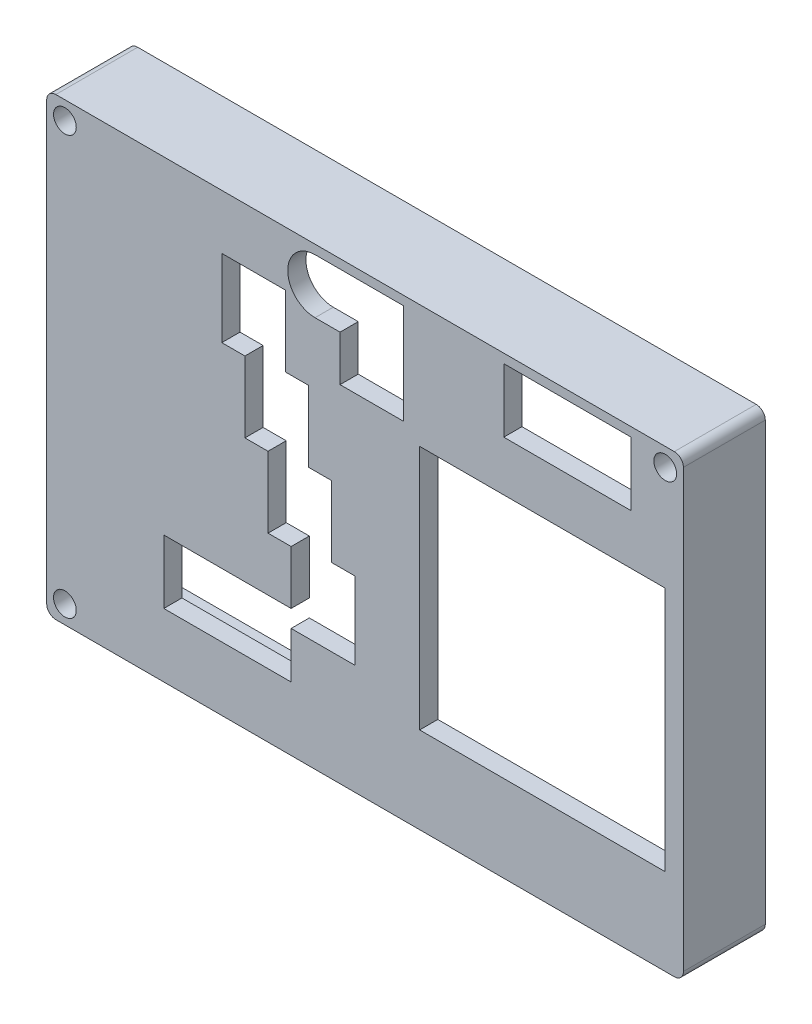
SolidWorks part; units mm, degrees
ref_plane "Front Plane" through (0, 0, 0) normal (0, 0, 1) x (1, 0, 0)
ref_plane "Top Plane" through (0, 0, 0) normal (0, 1, 0) x (1, 0, 0)
ref_plane "Right Plane" through (0, 0, 0) normal (1, 0, 0) x (0, 0, -1)
sketch "Sketch2" plane through (0, 0, 0) normal (0, 0, 1) x (1, 0, 0)
  line L0 (0, -55) -> (0, 55) construction
  line L1 (-35, 25) -> (35, 25)
  line L2 (-35, 25) -> (-35, -25)
  line L3 (-35, -25) -> (35, -25)
  line L4 (35, 25) -> (35, -25)
  line L5 (-35, 25) -> (35, -25) construction
  line L6 (-35, -25) -> (35, 25) construction
  line L7 (6, 11.5) -> (33, 11.5)
  line L8 (6, 11.5) -> (6, -15.5)
  line L9 (6, -15.5) -> (33, -15.5)
  line L10 (33, 11.5) -> (33, -15.5)
  line L11 (55, 0) -> (-55, 0) construction
  line L13 (-22.13, -11) -> (-8.13, -11)
  line L14 (-22.13, -11) -> (-22.13, -18)
  line L15 (-22.13, -18) -> (-8.13, -18)
  line L16 (-8.13, -12.9) -> (-8.13, -18)
  line L17 (-2.75, 24) -> (4.25, 24)
  line L19 (-2.75, 13) -> (4.25, 13)
  line L20 (4.25, 24) -> (4.25, 13)
  line L21 (-15.75, 19) -> (-8.75, 19)
  line L22 (-15.75, 19) -> (-15.75, 10.5)
  line L23 (-15.75, 10.5) -> (-13.21, 10.5)
  line L24 (-8.75, 19) -> (-8.75, 11.2)
  line L25 (-8.75, 11.2) -> (-6.21, 11.2)
  line L26 (-13.21, 10.5) -> (-13.21, 2.7)
  line L27 (-13.21, 2.7) -> (-10.67, 2.7)
  line L28 (-6.21, 11.2) -> (-6.21, 3.4)
  line L29 (-6.21, 3.4) -> (-3.67, 3.4)
  line L30 (-10.67, 2.7) -> (-10.67, -5.1)
  line L31 (-10.67, -5.1) -> (-8.13, -5.1)
  line L32 (-3.67, 3.4) -> (-3.67, -4.4)
  line L33 (-3.67, -4.4) -> (-1.13, -4.4)
  line L34 (-8.13, -5.1) -> (-8.13, -11)
  line L35 (-8.13, -12.9) -> (-1.13, -12.9)
  line L36 (-1.13, -4.4) -> (-1.13, -12.9)
  line L37 (15.25, 24) -> (29.25, 24)
  line L38 (15.25, 24) -> (15.25, 17)
  line L39 (15.25, 17) -> (29.25, 17)
  line L40 (29.25, 24) -> (29.25, 17)
  line L41 (-5.5, 24) -> (-2.75, 24)
  line L42 (-2.75, 18) -> (-2.75, 13)
  line L43 (-5.5, 18) -> (-2.75, 18)
  circle A0 centre (-33, 23) radius 1.25
  circle A1 centre (33, 23) radius 1.25
  circle A3 centre (-33, -23) radius 1.25
  arc A4 (-5.5, 24) -> (-5.5, 18) centre (-5.5, 21) ccw
  point P0 (0, 0)
  point P21 (-8.13, -11)
  point P22 (-8.13, -11.9024)
  point P27 (0, 0)
  dimension "D5" = 2.5
  dimension "D24" = 6
  dimension "D1" = 50
  dimension "D2" = 70
  dimension "D3" = 27
  dimension "D4" = 27
  dimension "D6" = 2
  dimension "D7" = 2
  dimension "D8" = 8.5
  dimension "D9" = 7
  dimension "D10" = 11
  dimension "D11" = 14
  dimension "D12" = 1
  dimension "D13" = 14
  dimension "D14" = 2.54
  dimension "D15" = 2.54
  dimension "D16" = 2.54
  dimension "D17" = 7.8
  dimension "D18" = 7.8
  dimension "D19" = 7.8
  dimension "D20" = 6
  dimension "D21" = 7
  dimension "D23" = 19.25
  dimension "D25" = 2.75
  dimension "D26" = 7
  dimension "D27" = 30.75
  dimension "D28" = 8.5
  dimension "D29" = 5.75
  dimension "D30" = 2
  dimension "D31" = 9.5
extrude "Boss-Extrude1" add sketch "Sketch2" along normal blind 2
sketch "Sketch4" plane through (0, 0, 0) normal (0, 0, -1) x (-1, 0, 0)
  line L1 (-30.9844, 24) -> (30.9844, 24)
  line L2 (-34, 20.9844) -> (-34, -24)
  line L4 (-35, 25) -> (-35, -25)
  line L5 (-35, -25) -> (35, -25)
  line L6 (35, -25) -> (35, 25)
  line L7 (35, 25) -> (-35, 25)
  line L8 (-35, 25) -> (-35, -25)
  line L9 (-35, -25) -> (35, -25)
  line L10 (35, -25) -> (35, 25)
  line L11 (35, 25) -> (-35, 25)
  line L12 (34, 20.9844) -> (34, -20.9844)
  line L24 (-34, -24) -> (30.9844, -24)
  circle A0 centre (-33, 23) radius 1.25 construction
  circle A1 centre (-33, 23) radius 1.25
  circle A2 centre (33, 23) radius 1.25 construction
  circle A3 centre (33, 23) radius 1.25
  circle A6 centre (33, -23) radius 1.25 construction
  circle A7 centre (33, -23) radius 1.25
  arc A10 (-34, 20.9844) -> (-30.9844, 24) centre (-33, 23) ccw
  arc A11 (30.9844, 24) -> (34, 20.9844) centre (33, 23) ccw
  circle A15 centre (-33, 23) radius 2.25 construction
  arc A16 (34, -20.9844) -> (30.9844, -24) centre (33, -23) ccw
  circle A17 centre (33, 23) radius 2.25 construction
  point P10 (-34, -23)
  point P11 (-34, -22.8583)
  point P13 (-34, -21.2125)
  point P19 (0, 0)
  point P20 (0, 0)
  point P21 (0, 0)
  point P22 (6.5104, 24)
  point P23 (30.75, 24)
  dimension "D9" = 1
  dimension "D2" = 1
  dimension "D3" = 1
  dimension "D4" = 1
  dimension "D5" = 1
  dimension "D1" = 0
  dimension "D6" = 1
  dimension "D7" = 1
extrude "Boss-Extrude2" add sketch "Sketch4" along normal blind 7
fillet "Fillet1" radius 1 4 edges at (35, -25, -2.5) (-35, -25, -2.5) (35, 25, -2.5) (-35, 25, -2.5)
